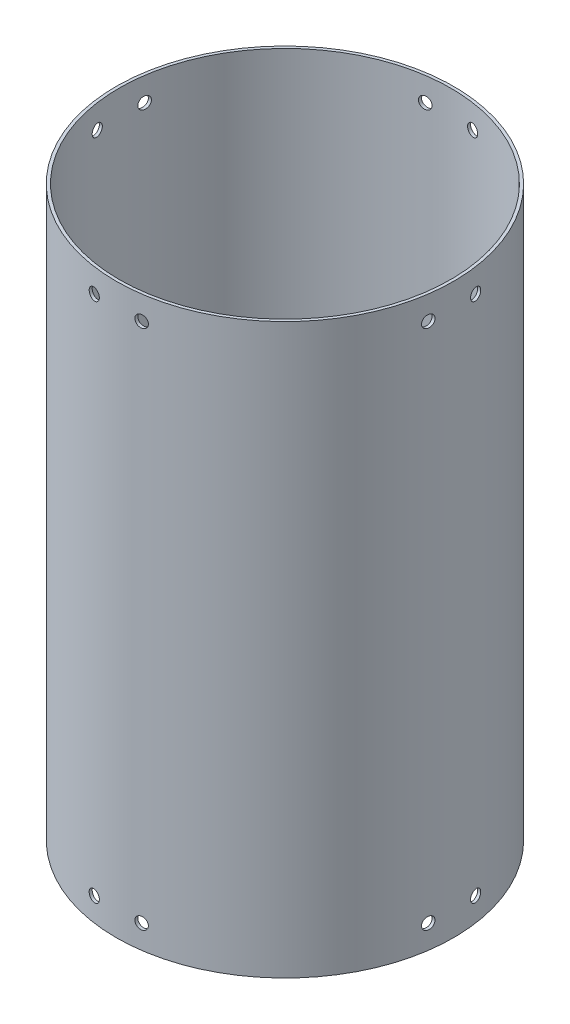
SolidWorks part; units mm, degrees
material "Carbon Fiber (2)"
ref_plane "Front Plane" through (0, 0, 0) normal (0, 0, 1) x (1, 0, 0)
ref_plane "Top Plane" through (0, 0, 0) normal (0, 1, 0) x (1, 0, 0)
ref_plane "Right Plane" through (0, 0, 0) normal (1, 0, 0) x (0, 0, -1)
sketch "Sketch1" plane through (0, 0, 0) normal (0, 1, 0) x (1, 0, 0)
  circle A0 centre (0, 0) radius 88.9
  circle A1 centre (0, 0) radius 90.4875
  dimension "D1" = 177.8
  dimension "D2" = 180.975
extrude "Boss-Extrude1" add sketch "Sketch1" along normal blind 304.8
ref_plane "Plane1" through (0, 0, -90.4875) normal (0, 0, -1) x (-1, 0, 0)
sketch "Sketch2" plane through (0, 0, -90.4875) normal (0, 0, -1) x (-1, 0, 0)
  line L0 (0, 0) -> (0, 304.8) construction
  line L1 (0, 292.1) -> (-12.7, 292.1) construction
  line L2 (0, 292.1) -> (12.7, 292.1) construction
  line L3 (0, 0) -> (0, 12.7) construction
  line L5 (12.7, 12.7) -> (0, 12.7) construction
  line L6 (0, 12.7) -> (-12.7, 12.7) construction
  circle A0 centre (-12.7, 292.1) radius 3.175
  circle A1 centre (12.7, 292.1) radius 3.175
  circle A2 centre (-12.7, 12.7) radius 3.175
  circle A3 centre (12.7, 12.7) radius 3.175
  dimension "D5" = 6.35
  dimension "D9" = 6.35
  dimension "D1" = 304.8
  dimension "D2" = 12.7
  dimension "D3" = 12.7
  dimension "D4" = 12.7
  dimension "D6" = 12.7
  dimension "D7" = 12.7
  dimension "D8" = 12.7
extrude "Cut-Extrude1" cut sketch "Sketch2" against normal blind 25.4
pattern_circular "CirPattern1" count 4 over 360 about axis through (0, 304.8, 0) along (0, 1, 0) of "Cut-Extrude1"
